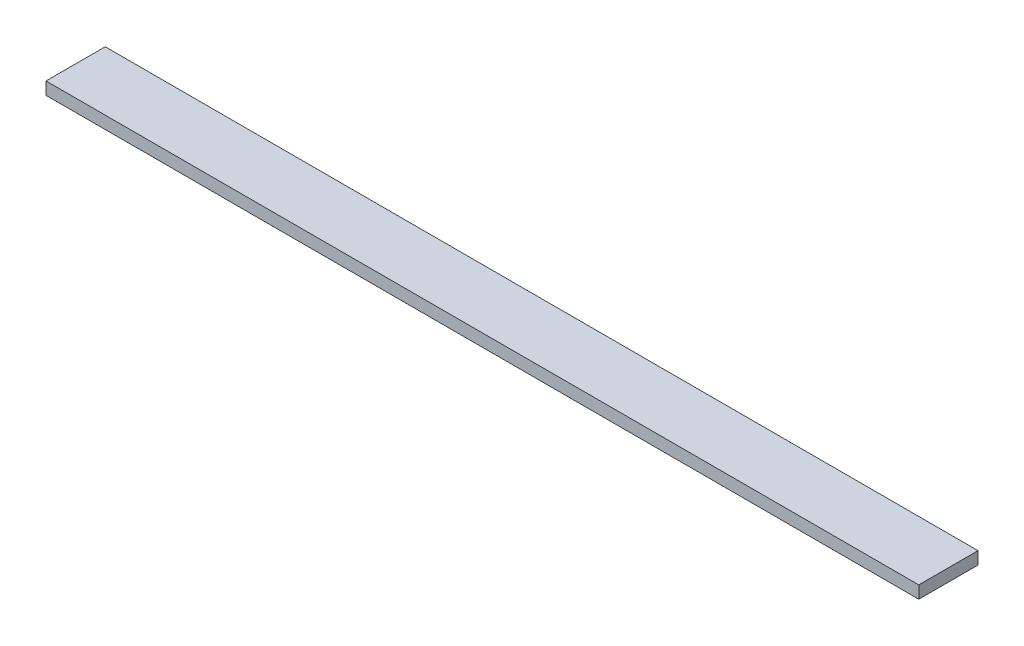
SolidWorks part; units mm, degrees
ref_plane "Front Plane" through (0, 0, 0) normal (0, 0, 1) x (1, 0, 0)
ref_plane "Top Plane" through (0, 0, 0) normal (0, 1, 0) x (1, 0, 0)
ref_plane "Right Plane" through (0, 0, 0) normal (1, 0, 0) x (0, 0, -1)
sketch "Sketch1" plane through (0, 0, 0) normal (0, 1, 0) x (1, 0, 0)
  line L1 (0, 0) -> (177.8, 0)
  line L2 (0, 0) -> (0, 12.065)
  line L3 (0, 12.065) -> (177.8, 12.065)
  line L4 (177.8, 0) -> (177.8, 12.065)
  dimension "D1" = 12.065
  dimension "D2" = 177.8
extrude "Boss-Extrude1" add sketch "Sketch1" along normal blind 2.54
